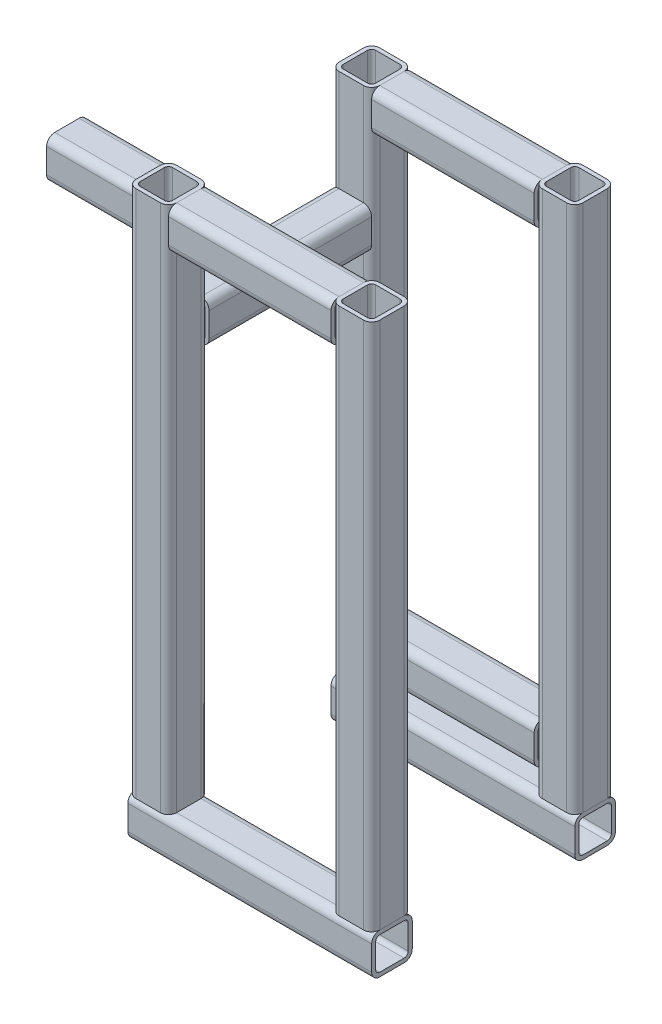
SolidWorks part; units mm, degrees
ref_plane "Front Plane" through (0, 0, 0) normal (0, 0, 1) x (1, 0, 0)
ref_plane "Top Plane" through (0, 0, 0) normal (0, 1, 0) x (1, 0, 0)
ref_plane "Right Plane" through (0, 0, 0) normal (1, 0, 0) x (0, 0, -1)
sketch3d "3DSketch1"
  line L0 (0, 0, 0) -> (0, 520, 0)
  line L1 (0, 0, 0) -> (0, 0, 200) construction
  line L2 (0, 0, 200) -> (0, 520, 200)
  line L3 (0, 420, 200) -> (0, 420, 0)
  line L4 (0, 0, 200) -> (224.8034, 0, 200) construction
  line L5 (0, 0, 0) -> (648.8185, 0, 0) construction
  line L6 (0, 0, 200) -> (200, 0, 200)
  line L7 (0, 0, 0) -> (200, 0, 0)
  line L8 (200, 0, 200) -> (200, 520, 200)
  line L9 (200, 0, 0) -> (200, 520, 0)
  line L10 (0, 520, 200) -> (200, 520, 200)
  line L11 (0, 520, 0) -> (200, 520, 0)
  line L12 (0, 420, 100) -> (-200, 420, 100)
  line L13 (200, 60, 0) -> (0, 60, 0)
  line L14 (200, 520, 0) -> (200, 520, 200)
  dimension "D1" = 520
  dimension "D2" = 200
  dimension "D3" = 520
  dimension "D4" = 100
  dimension "D5" = 200
  dimension "D6" = 0
  dimension "D7" = 0
  dimension "D8" = 200
  dimension "D9" = 200
  dimension "D10" = 60
other "Square tube 40 X 40 X 4(1)"
ref_plane "Plane2" through (0, 0, 200) normal (1, 0, 0) x (0, 0, -1)
sketch "Sketch1" plane through (0, 0, 200) normal (1, 0, 0) x (0, 0, -1)
  line L0 (-12, -16) -> (12, -16)
  line L1 (-16, -12) -> (-16, 12)
  line L2 (12, 16) -> (-12, 16)
  line L3 (16, 12) -> (16, -12)
  line L4 (-12, -20) -> (12, -20)
  line L5 (-20, -12) -> (-20, 12)
  line L6 (12, 20) -> (-12, 20)
  line L7 (20, 12) -> (20, -12)
  arc A0 (20, 12) -> (12, 20) centre (12, 12) ccw
  arc A1 (12, -20) -> (20, -12) centre (12, -12) ccw
  arc A2 (-20, -12) -> (-12, -20) centre (-12, -12) ccw
  arc A3 (-12, 20) -> (-20, 12) centre (-12, 12) ccw
  arc A4 (-12, 16) -> (-16, 12) centre (-12, 12) ccw
  arc A5 (16, 12) -> (12, 16) centre (12, 12) ccw
  arc A6 (12, -16) -> (16, -12) centre (12, -12) ccw
  arc A7 (-16, -12) -> (-12, -16) centre (-12, -12) ccw
  point P0 (-20, 0)
  point P1 (20, 0)
  point P2 (0, 20)
  point P3 (0, -20)
  point P4 (0, 0)
  point P5 (-20, -20)
  point P6 (20, -20)
  point P7 (20, 20)
  point P8 (-20, 20)
  point P33 (0, 0)
  dimension "D1" = 8
  dimension "Thickness" = 4
  dimension "V_leg" = 40
sketch "Sketch12" plane through (0, 0, 20) normal (0, 0, 1) x (1, 0, 0)
  line L0 (612.5804, 142.5218) -> (-597.304, 142.5218) construction
  line L1 (612.5804, 142.5218) -> (-597.304, 142.5218)
